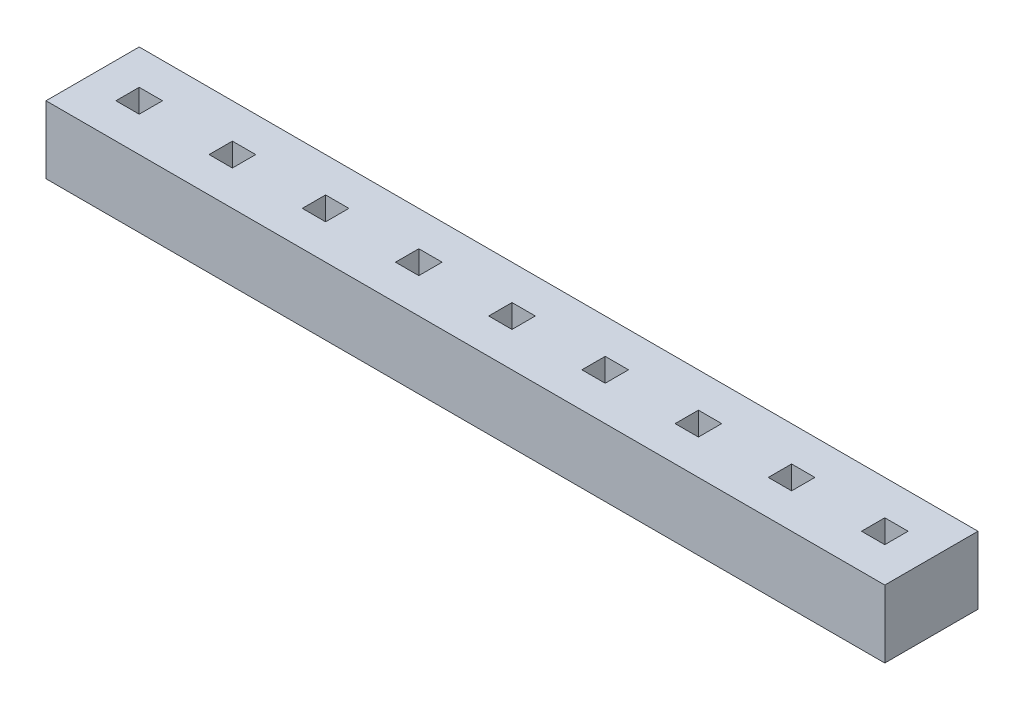
SolidWorks part; units mm, degrees
ref_plane "Front Plane" through (0, 0, 0) normal (0, 0, 1) x (1, 0, 0)
ref_plane "Top Plane" through (0, 0, 0) normal (0, 1, 0) x (1, 0, 0)
ref_plane "Right Plane" through (0, 0, 0) normal (1, 0, 0) x (0, 0, -1)
sketch "Sketch1" plane through (0, 0, 0) normal (0, 1, 0) x (1, 0, 0)
  line L1 (0, 0) -> (18, 0)
  line L2 (0, 0) -> (0, 2)
  line L3 (0, 2) -> (18, 2)
  line L4 (18, 0) -> (18, 2)
extrude "Boss-Extrude1" add sketch "Sketch1" along normal blind 1.45
sketch "Sketch2" plane through (0, 1.45, 0) normal (0, 1, 0) x (1, 0, 0)
  line L0 (2.75, 0.75) -> (3.25, 0.75)
  line L1 (0.75, 0.75) -> (1.25, 0.75)
  line L2 (0.75, 0.75) -> (0.75, 1.25)
  line L3 (0.75, 1.25) -> (1.25, 1.25)
  line L4 (1.25, 0.75) -> (1.25, 1.25)
  line L5 (2.75, 0.75) -> (2.75, 1.25)
  line L6 (2.75, 1.25) -> (3.25, 1.25)
  line L7 (3.25, 0.75) -> (3.25, 1.25)
  line L8 (4.75, 0.75) -> (5.25, 0.75)
  line L9 (4.75, 0.75) -> (4.75, 1.25)
  line L10 (4.75, 1.25) -> (5.25, 1.25)
  line L11 (5.25, 0.75) -> (5.25, 1.25)
  line L12 (6.75, 0.75) -> (7.25, 0.75)
  line L13 (6.75, 0.75) -> (6.75, 1.25)
  line L14 (6.75, 1.25) -> (7.25, 1.25)
  line L15 (7.25, 0.75) -> (7.25, 1.25)
  line L16 (8.75, 0.75) -> (9.25, 0.75)
  line L17 (8.75, 0.75) -> (8.75, 1.25)
  line L18 (8.75, 1.25) -> (9.25, 1.25)
  line L19 (9.25, 0.75) -> (9.25, 1.25)
  line L20 (10.75, 0.75) -> (11.25, 0.75)
  line L21 (10.75, 0.75) -> (10.75, 1.25)
  line L22 (10.75, 1.25) -> (11.25, 1.25)
  line L23 (11.25, 0.75) -> (11.25, 1.25)
  line L24 (12.75, 0.75) -> (13.25, 0.75)
  line L25 (12.75, 0.75) -> (12.75, 1.25)
  line L26 (12.75, 1.25) -> (13.25, 1.25)
  line L27 (13.25, 0.75) -> (13.25, 1.25)
  line L28 (14.75, 0.75) -> (15.25, 0.75)
  line L29 (14.75, 0.75) -> (14.75, 1.25)
  line L30 (14.75, 1.25) -> (15.25, 1.25)
  line L31 (15.25, 0.75) -> (15.25, 1.25)
  line L32 (16.75, 0.75) -> (17.25, 0.75)
  line L33 (16.75, 0.75) -> (16.75, 1.25)
  line L34 (16.75, 1.25) -> (17.25, 1.25)
  line L35 (17.25, 0.75) -> (17.25, 1.25)
  dimension "D1" = 9
extrude "Cut-Extrude1" cut sketch "Sketch2" against normal blind 1.45
